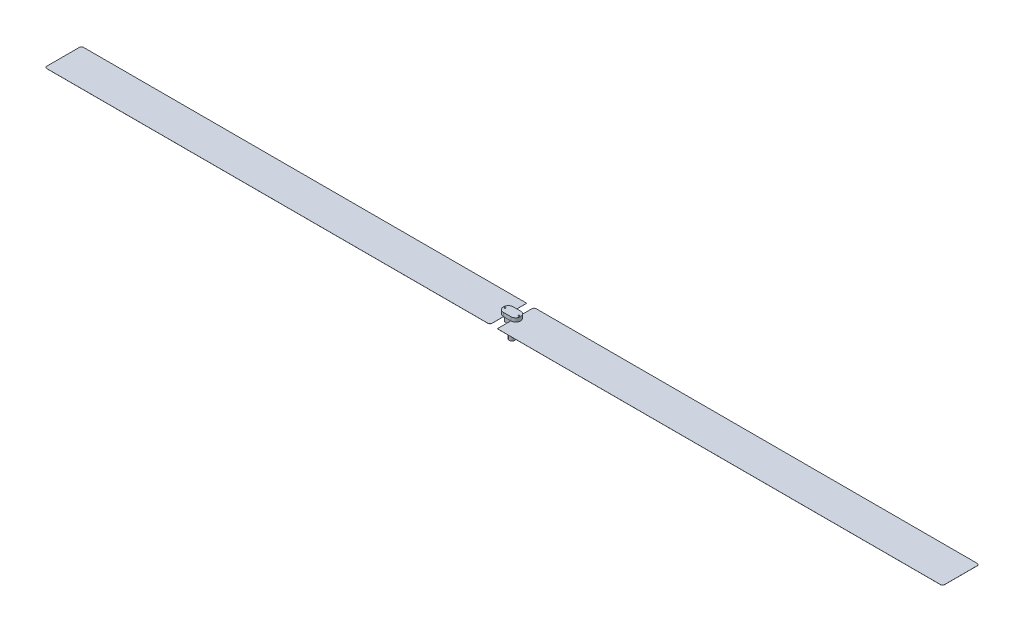
SolidWorks part; units mm, degrees
ref_plane "Front Plane" through (0, 0, 0) normal (0, 0, 1) x (1, 0, 0)
ref_plane "Top Plane" through (0, 0, 0) normal (0, 1, 0) x (1, 0, 0)
ref_plane "Right Plane" through (0, 0, 0) normal (1, 0, 0) x (0, 0, -1)
sketch "Sketch1" plane through (0, 0, 0) normal (0, 1, 0) x (1, 0, 0)
  circle A0 centre (0, 0) radius 0.3
  circle A1 centre (0, 0) radius 0.377
  dimension "D1" = 0.6
extrude "Boss-Extrude1" add sketch "Sketch1" along normal blind 2
sketch "Sketch2" plane through (0, 2, 0) normal (0, 1, 0) x (1, 0, 0)
  line L1 (-0.5, -0.5) -> (0.5, -0.5)
  line L2 (-0.5, -0.5) -> (-0.5, 0.5)
  line L3 (-0.5, 0.5) -> (0.5, 0.5)
  line L4 (0.5, -0.5) -> (0.5, 0.5)
  line L5 (-0.5, -0.5) -> (0.5, 0.5) construction
  line L6 (-0.5, 0.5) -> (0.5, -0.5) construction
  point P0 (0, 0)
  dimension "D1" = 1
  dimension "D2" = 1
extrude "Boss-Extrude2" add sketch "Sketch2" along normal blind 0.7
sketch "Sketch3" plane through (0, 2.7, 0) normal (0, 1, 0) x (1, 0, 0)
  line L0 (-0.5, 0) -> (0.5, 0) construction
  line L1 (-0.5, 0.5) -> (-0.5, -0.5) construction
  line L2 (0.5, -0.5) -> (0.5, 0.5) construction
  line L3 (-0.5, 0.6624) -> (0.5, 0.6624)
  line L4 (-0.5, -0.6624) -> (0.5, -0.6624)
  arc A0 (-0.5, 0.6624) -> (-0.5, -0.6624) centre (-0.5, 0) ccw
  arc A1 (0.5, -0.6624) -> (0.5, 0.6624) centre (0.5, 0) ccw
  point P6 (0, 0)
extrude "Boss-Extrude3" add sketch "Sketch3" along normal blind 0.5
sketch "Sketch4" plane through (0, 3.2, 0) normal (0, 1, 0) x (1, 0, 0)
  line L0 (0, 0.8067) -> (0, -0.9213) construction
  circle A0 centre (-0.9416, 0) radius 0.1
  circle A1 centre (0.9416, 0) radius 0.1
extrude "Cut-Extrude2" cut sketch "Sketch4" against normal blind 0.4
sketch "Sketch5" plane through (0, 2.7, 0) normal (0, -1, 0) x (1, 0, 0)
  line L0 (0.5, 0.5) -> (0.5, -0.5) construction
  line L1 (0.8, -2.5) -> (60.8, -2.5)
  line L2 (0.5, -2.2) -> (0.5, 2.5)
  line L3 (0.5, 2.5) -> (60.8, 2.5)
  line L4 (61.1, -2.2) -> (61.1, 2.2)
  line L5 (-1.9899, 0) -> (8.6367, 0) construction
  line L6 (0, 1.3705) -> (0, -1.8368) construction
  line L7 (-0.8, 2.5) -> (-60.8, 2.5)
  line L8 (-61.1, -2.2) -> (-61.1, 2.2)
  line L9 (-0.8, -2.5) -> (-60.8, -2.5)
  line L10 (-0.5, -2.2) -> (-0.5, 2.2)
  line L11 (-0.8, -2.5) -> (-0.5, -2.5)
  line L12 (-0.5, -0.5) -> (-0.5, 0.5) construction
  line L13 (-0.5, -2.5) -> (-0.5, -2.2)
  arc A0 (61.1, 2.2) -> (60.8, 2.5) centre (60.8, 2.2) ccw
  arc A1 (60.8, -2.5) -> (61.1, -2.2) centre (60.8, -2.2) ccw
  arc A2 (0.8, -2.5) -> (0.5, -2.2) centre (0.8, -2.2) cw
  arc A3 (-61.1, 2.2) -> (-60.8, 2.5) centre (-60.8, 2.2) cw
  arc A4 (-60.8, -2.5) -> (-61.1, -2.2) centre (-60.8, -2.2) cw
  arc A6 (-0.5, 2.2) -> (-0.8, 2.5) centre (-0.8, 2.2) ccw
  point P15 (0.5, -2.5)
  point P32 (-0.5, 2.5)
  dimension "D1" = 0.3
  dimension "D2" = 0.3
  dimension "D3" = 0.3
  dimension "D4" = 0.3
  dimension "D5" = 60
  dimension "D6" = 5
extrude "Boss-Extrude4" add sketch "Sketch5" along normal blind 0.01
